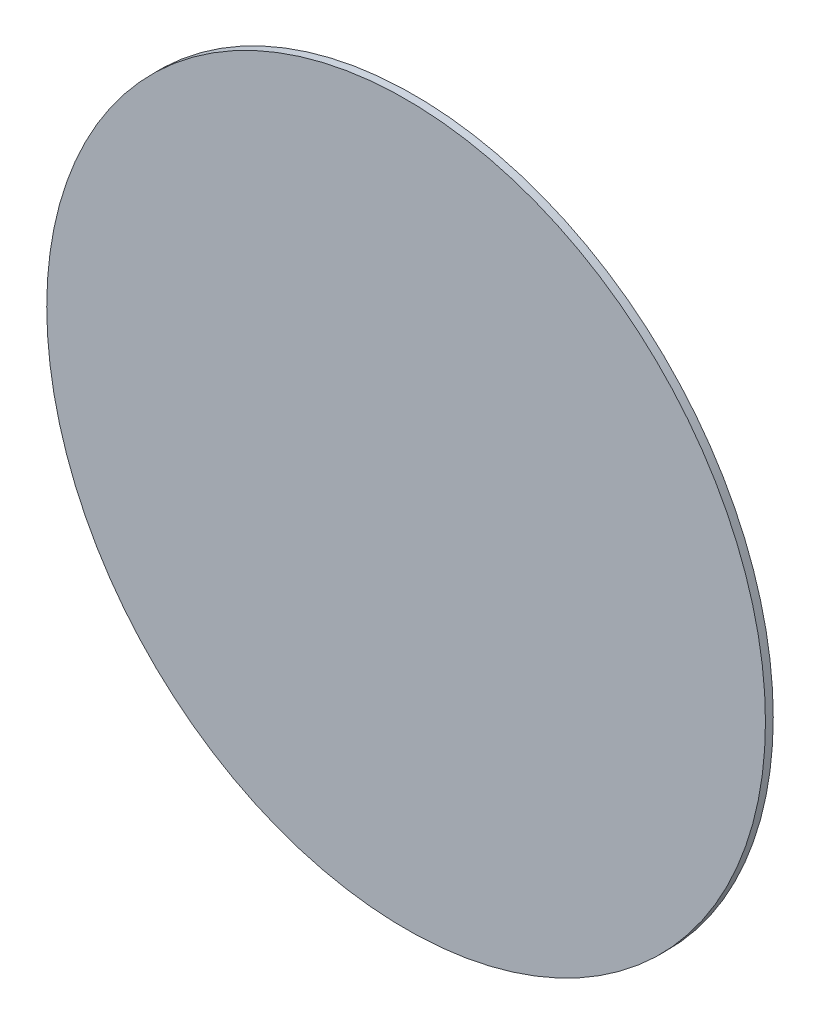
SolidWorks part; units mm, degrees
ref_plane "Front Plane" through (0, 0, 0) normal (0, 0, 1) x (1, 0, 0)
ref_plane "Top Plane" through (0, 0, 0) normal (0, 1, 0) x (1, 0, 0)
ref_plane "Right Plane" through (0, 0, 0) normal (1, 0, 0) x (0, 0, -1)
sketch "Sketch1" plane through (0, 0, 0) normal (0, 0, 1) x (1, 0, 0)
  circle A0 centre (0, 0) radius 46
  dimension "D1" = 92
extrude "Boss-Extrude1" add sketch "Sketch1" along normal blind 1
